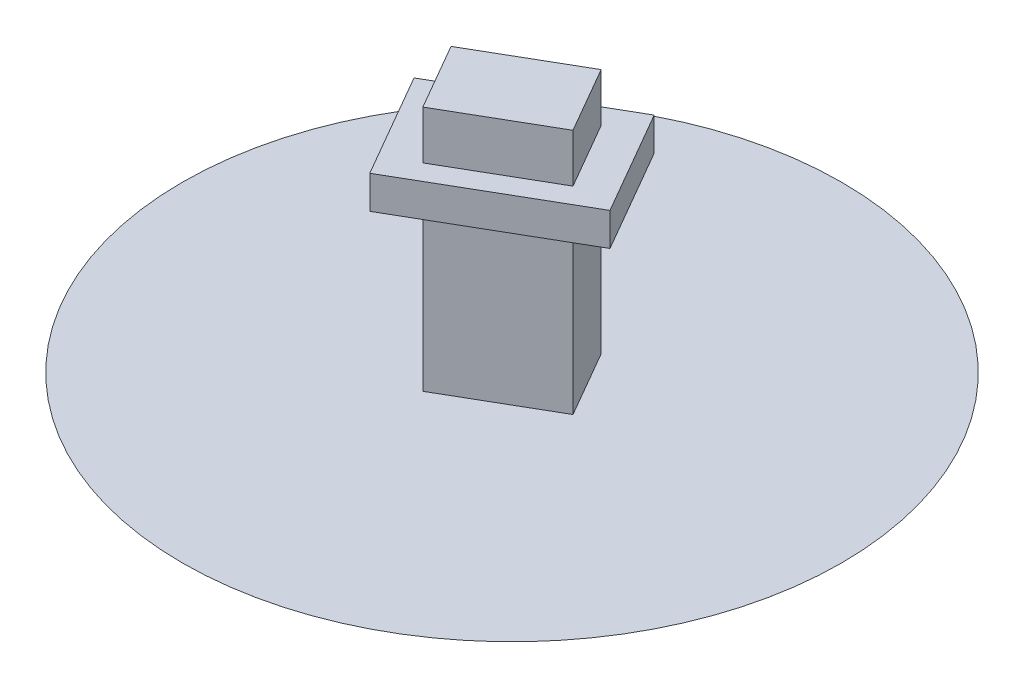
SolidWorks part; units mm, degrees
ref_plane "Front" through (0, 0, 0) normal (0, 0, 1) x (1, 0, 0)
ref_plane "Top" through (0, 0, 0) normal (0, 1, 0) x (1, 0, 0)
ref_plane "Right" through (0, 0, 0) normal (1, 0, 0) x (0, 0, -1)
sketch "Sketch1" plane through (0, 0, 0) normal (0, 1, 0) x (1, 0, 0)
  line L0 (0, 0) -> (-8660.254, -5000)
  line L1 (-8660.254, -5000) -> (-5160.254, -11062.1778)
  line L2 (-5160.254, -11062.1778) -> (3500, -6062.1778)
  line L3 (3500, -6062.1778) -> (0, 0)
  line L4 (0, 0) -> (-51.8966, 0) construction
  dimension "D1" = 30
  dimension "D2" = 7000
  dimension "D3" = 10000
extrude "Extrude1" add sketch "Sketch1" along normal blind 15000
sketch "Sketch2" plane through (0, 15000, 0) normal (0, 1, 0) x (-1, 0, 0)
  line L0 (0, 0) -> (-3500, 6062.1778) construction
  line L1 (-3500, 6062.1778) -> (5160.254, 11062.1778) construction
  line L2 (5160.254, 11062.1778) -> (8660.254, 5000) construction
  line L3 (8660.254, 5000) -> (0, 0) construction
  line L4 (12258.3302, 4767.9492) -> (-1598.0762, -3232.0508)
  line L5 (-7098.0762, 6294.2286) -> (6758.3302, 14294.2286)
  line L6 (-1598.0762, -3232.0508) -> (-7098.0762, 6294.2286)
  line L7 (6758.3302, 14294.2286) -> (12258.3302, 4767.9492)
  line L8 (-4500, 7794.2286) -> (4160.254, 12794.2286) construction
  line L9 (7758.3302, 12562.1778) -> (11258.3302, 6500) construction
  line L10 (-2598.0762, -1500) -> (-6098.0762, 4562.1778) construction
  line L11 (9660.254, 3267.9492) -> (1000, -1732.0508) construction
extrude "Extrude2" add sketch "Sketch2" along normal blind 3000
sketch "Sketch3" plane through (0, 18000, 0) normal (0, 1, 0) x (-1, 0, 0)
  line L0 (0, 0) -> (-3500, 6062.1778)
  line L1 (-3500, 6062.1778) -> (5160.254, 11062.1778)
  line L2 (5160.254, 11062.1778) -> (8660.254, 5000)
  line L3 (8660.254, 5000) -> (0, 0)
extrude "Extrude3" add sketch "Sketch3" along normal blind 4400
sketch "Sketch4" plane through (0, 0, 0) normal (0, 1, 0) x (1, 0, 0)
  line L0 (-8660.254, -5000) -> (3500, -6062.1778) construction
  circle A0 centre (-2580.127, -5531.0889) radius 30000
  dimension "D1" = 60000
extrude "Extrude4" add sketch "Sketch4" along normal blind 0.01
